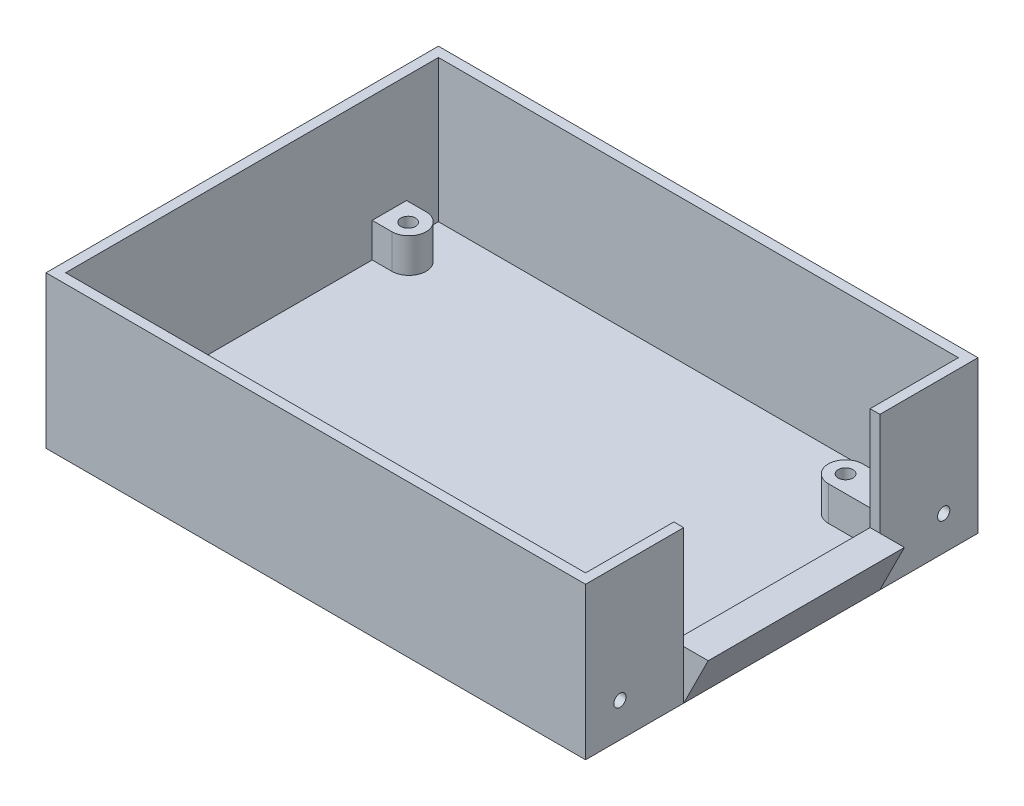
SolidWorks part; units mm, degrees
ref_plane "Front Plane" through (0, 0, 0) normal (0, 0, 1) x (1, 0, 0)
ref_plane "Top Plane" through (0, 0, 0) normal (0, 1, 0) x (1, 0, 0)
ref_plane "Right Plane" through (0, 0, 0) normal (1, 0, 0) x (0, 0, -1)
sketch "Sketch5" plane through (0, 0, 0) normal (0, 1, 0) x (1, 0, 0)
  line L1 (-80, 83.5762) -> (30, 83.5762)
  line L2 (-80, 83.5762) -> (-80, 3.5762)
  line L3 (-80, 3.5762) -> (30, 3.5762)
  line L4 (30, 83.5762) -> (30, 3.5762)
  dimension "D1" = 80
  dimension "D2" = 110
extrude "Boss-Extrude8" add sketch "Sketch5" along normal blind 2
sketch "Sketch9" plane through (0, 2, 0) normal (0, 1, 0) x (1, 0, 0)
  circle A0 centre (-74, 15.5762) radius 3.5
  circle A1 centre (-74, 71.5762) radius 3.5
  circle A2 centre (15, 15.5762) radius 3.5
  circle A3 centre (15, 71.5762) radius 3.5
  dimension "D1" = 56
  dimension "D2" = 89
extrude "Boss-Extrude11" add sketch "Sketch9" along normal blind 7 contours A2 | A3 | A1 | A0
sketch "Sketch11" plane through (0, 9, 0) normal (0, 1, 0) x (1, 0, 0)
  circle A0 centre (-74, 15.5762) radius 1.5
  circle A1 centre (-74, 15.5762) radius 3.5 construction
  circle A2 centre (-74, 71.4053) radius 1.5
  circle A3 centre (15, 71.5762) radius 1.5
  circle A4 centre (15, 15.5762) radius 1.5
extrude "Cut-Extrude1" cut sketch "Sketch11" against normal blind 7
sketch "Sketch12" plane through (0, 2, 0) normal (0, 1, 0) x (1, 0, 0)
  line L1 (-80, 3.5762) -> (30, 3.5762)
  line L2 (-80, 3.5762) -> (-80, 83.5762)
  line L3 (-80, 83.5762) -> (30, 83.5762)
  line L4 (30, 3.5762) -> (30, 83.5762)
  line L5 (-78, 5.5762) -> (28, 5.5762)
  line L6 (-78, 5.5762) -> (-78, 81.5762)
  line L7 (-78, 81.5762) -> (28, 81.5762)
  line L8 (28, 5.5762) -> (28, 81.5762)
  dimension "D1" = 2
  dimension "D2" = 2
  dimension "D3" = 2
  dimension "D4" = 2
extrude "Boss-Extrude12" add sketch "Sketch12" along normal blind 29
sketch "Sketch13" plane through (30, 0, 0) normal (1, 0, 0) x (0, 0, -1)
  line L0 (3.205, 195.1644) -> (2.4234, 203.7937)
sketch "Sketch14" plane through (0, 2, 0) normal (0, 1, 0) x (1, 0, 0)
  line L0 (-74, 12.0762) -> (-78, 12.0762)
  line L1 (-78, 81.5762) -> (-78, 5.5762) construction
  line L2 (-74, 19.0762) -> (-78, 19.0762)
  line L3 (-78, 19.0762) -> (-78, 12.0762)
  line L4 (-74, 19.0762) -> (-77.5, 15.5762)
  line L5 (-77.5, 15.5762) -> (-74, 12.0762)
  circle A0 centre (-74, 15.5762) radius 3.5 construction
extrude "Boss-Extrude14" add sketch "Sketch14" along normal blind 7
sketch "Sketch15" plane through (0, 2, 0) normal (0, 1, 0) x (1, 0, 0)
  line L0 (-74, 75.0762) -> (-78, 75.0762)
  line L1 (-78, 81.5762) -> (-78, 19.0762) construction
  line L2 (-74, 68.0762) -> (-78, 68.0762)
  line L3 (-78, 68.0762) -> (-78, 75.0762)
  line L4 (-74, 75.0762) -> (-77.5, 71.5762)
  line L5 (-77.5, 71.5762) -> (-74, 68.0762)
  circle A0 centre (-74, 71.5762) radius 3.5 construction
extrude "Boss-Extrude15" add sketch "Sketch15" along normal blind 7
sketch "Sketch16" plane through (30, 0, 0) normal (1, 0, 0) x (0, 0, -1)
  line L0 (43.5762, 31) -> (43.5762, 0) construction
  line L1 (3.5762, 31) -> (83.5762, 31) construction
  line L2 (3.5762, 0) -> (83.5762, 0) construction
  line L4 (23.5762, 31) -> (63.5762, 31)
  line L5 (23.5762, 31) -> (23.5762, 10)
  line L6 (23.5762, 10) -> (63.5762, 10)
  line L7 (63.5762, 31) -> (63.5762, 10)
  dimension "D1" = 40
  dimension "D2" = 10
extrude "Cut-Extrude2" cut sketch "Sketch16" against normal up to next contours L5 L4 L7 L6
sketch "Sketch17" plane through (0, 2, 0) normal (0, 1, 0) x (1, 0, 0)
  line L0 (15, 75.0762) -> (28, 75.0762)
  line L1 (28, 63.5762) -> (28, 81.5762) construction
  line L2 (15, 68.0762) -> (28, 68.0762)
  line L3 (28, 5.5762) -> (28, 81.5762) construction
  line L4 (28, 68.0762) -> (28, 75.0762)
  line L5 (15, 75.0762) -> (18.5, 71.5762)
  line L6 (18.5, 71.5762) -> (15, 68.0762)
  circle A0 centre (15, 71.5762) radius 3.5 construction
  circle A1 centre (15, 71.5762) radius 3.5 construction
extrude "Boss-Extrude16" add sketch "Sketch17" along normal blind 7
sketch "Sketch18" plane through (0, 2, 0) normal (0, 1, 0) x (1, 0, 0)
  line L0 (15, 19.0762) -> (28, 19.0762)
  line L1 (28, 5.5762) -> (28, 23.5762) construction
  line L2 (28, 19.0762) -> (28, 12.0762)
  line L3 (28, 12.0762) -> (15, 12.0762)
  line L4 (15, 12.0762) -> (18.5, 15.5762)
  line L5 (18.5, 15.5762) -> (15, 19.0762)
  circle A0 centre (15, 15.5762) radius 3.5 construction
  circle A1 centre (15, 15.5762) radius 3.5 construction
extrude "Boss-Extrude17" add sketch "Sketch18" along normal blind 7
sketch "Sketch22" plane through (0, 0, -63.5762) normal (0, 0, 1) x (1, 0, 0)
  line L0 (30, 10) -> (35, 10)
  line L1 (30, 10) -> (30, 0)
  line L2 (30, 0) -> (35, 10)
extrude "Boss-Extrude18" add sketch "Sketch22" along normal up to vertex (40 mm away)
sketch "Sketch23" plane through (30, 0, 0) normal (1, 0, 0) x (0, 0, -1)
  line L0 (3.5762, 0) -> (23.5762, 0) construction
  line L1 (3.5762, 31) -> (3.5762, 0) construction
  circle A0 centre (10.5762, 7) radius 1.25
  point P2 (0, 0)
  dimension "D1" = 7
  dimension "D2" = 7
extrude "Cut-Extrude4" cut sketch "Sketch23" against normal up to next
sketch "Sketch24" plane through (30, 0, 0) normal (1, 0, 0) x (0, 0, -1)
  line L2 (63.5762, 0) -> (83.5762, 0) construction
  line L3 (83.5762, 31) -> (83.5762, 0) construction
  circle A0 centre (76.5762, 7) radius 1.25
  point P2 (67.5965, -2.4741)
  point P3 (0, 0)
  point P4 (0, 0)
  point P5 (0, 0)
  point P6 (0, 0)
  dimension "D1" = 7
  dimension "D2" = 7
extrude "Cut-Extrude5" cut sketch "Sketch24" against normal up to next
